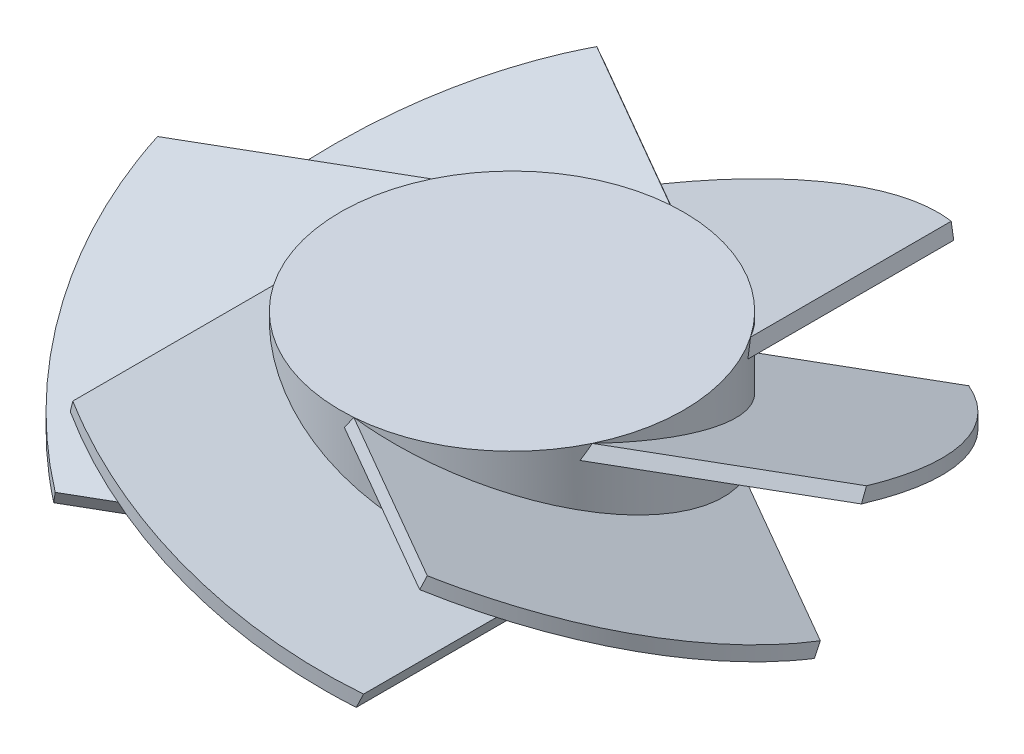
SolidWorks part; units mm, degrees
ref_plane "Front Plane" through (0, 0, 0) normal (0, 0, 1) x (1, 0, 0)
ref_plane "Top Plane" through (0, 0, 0) normal (0, 1, 0) x (1, 0, 0)
ref_plane "Right Plane" through (0, 0, 0) normal (1, 0, 0) x (0, 0, -1)
sketch "Sketch1" plane through (0, 0, 0) normal (0, 1, 0) x (1, 0, 0)
  circle A0 centre (0, 0) radius 25
extrude "Boss-Extrude1" add sketch "Sketch1" along normal blind 18
ref_plane "Plane1" through (0, 0, 48) normal (0, 0, -1) x (-1, 0, 0)
sketch "Sketch3" plane through (0, 0, 48) normal (0, 0, -1) x (-1, 0, 0)
  line L0 (-25, 9) -> (25, 9) construction
  line L1 (-25, 18) -> (-25, 0) construction
  line L2 (25, 0) -> (25, 18) construction
  line L3 (0, 0) -> (0, 18) construction
  line L4 (25, 18) -> (-25, 18) construction
  line L5 (-21.3628, 1.8671) -> (20.6458, 18)
  line L7 (-20.6458, 0) -> (21.3628, 16.1329)
  line L8 (-21.3628, 1.8671) -> (-20.6458, 0)
  line L9 (20.6458, 18) -> (21.3628, 16.1329)
  line L10 (-21.3628, 1.8671) -> (21.3628, 16.1329) construction
  line L11 (-20.6458, 0) -> (20.6458, 18) construction
  line L12 (27.5, 0) -> (-27.5, 0) construction
  point P13 (21.9714, 18)
  point P14 (0, 9)
  point P17 (0, 9)
  point P18 (0, 9)
  point P19 (-22.2858, -1.857)
  point P20 (20.8932, 18)
  point P21 (-22.2858, -1.857)
  point P22 (0, 0)
  point P23 (0, 0)
  point P24 (-22.2858, -1.857)
  point P25 (-22.2858, -1.857)
  point P26 (0, 0)
  point P27 (-22.2673, -1.857)
  point P28 (0, 0)
  point P29 (0, 0)
  point P30 (22.103, 18)
  point P31 (-22.1542, -1.857)
  point P32 (0, 0)
  point P33 (0, 0)
  point P34 (0, 0)
  point P35 (0, 0)
  point P36 (-22.1542, -1.857)
  point P37 (-22.1542, -1.857)
  point P38 (-25, 0)
  point P39 (-23.8564, 1.9578)
  point P40 (-23.2521, 0)
  point P43 (0, 0)
  dimension "D1" = 45
  dimension "D2" = 2
extrude "Boss-Extrude2" add sketch "Sketch3" along normal blind 38
pattern_circular "CirPattern1" count 6 over 360 about axis through (0, 0, 0) along (0, 1, 0) of "Boss-Extrude2"
sketch "Sketch4" plane through (0, 18, 0) normal (0, 1, 0) x (1, 0, 0)
  circle A0 centre (0, 0) radius 48
  circle A1 centre (0, 0) radius 55.206
extrude "Cut-Extrude2" cut sketch "Sketch4" against normal blind 38
